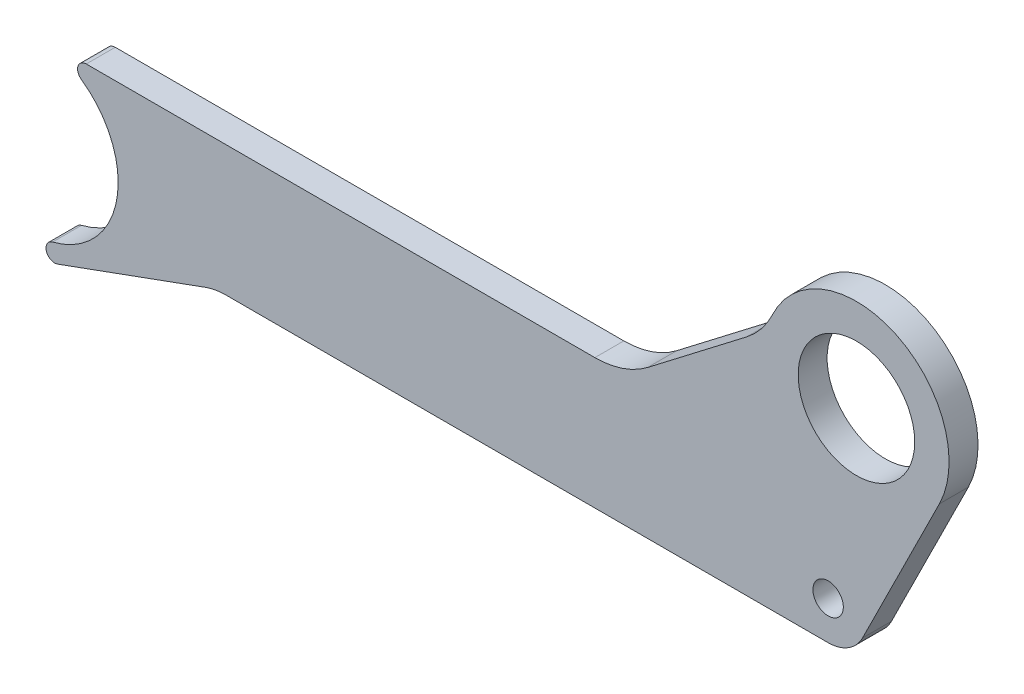
SolidWorks part; units mm, degrees
ref_plane "Plane1" through (0, 0, 0) normal (0, 0, 1) x (1, 0, 0)
ref_plane "Plane2" through (0, 0, 0) normal (0, 1, 0) x (1, 0, 0)
ref_plane "Plane3" through (0, 0, 0) normal (1, 0, 0) x (0, 0, -1)
sketch "Sketch1" plane through (0, 0, 0) normal (0, 0, 1) x (1, 0, 0)
  line L0 (-37.9234, 2.4122) -> (-72.0845, -23.8006)
  line L1 (-90.3474, -30) -> (-266.0263, -30)
  line L2 (2.1045, -67.6387) -> (28.6531, -14.2478)
  line L3 (-217.9327, -75) -> (-9.7772, -75)
  line L4 (-9.7772, -61.7305) -> (0, 0) construction
  line L5 (0, 0) -> (134, 0) construction
  line L8 (-275.9117, -94.8191) -> (-224.7731, -76.2061)
  line L9 (0, 0) -> (-76.4334, -58.6494) construction
  circle A0 centre (0, 0) radius 20.125
  arc A1 (28.6531, -14.2478) -> (-28.9993, 13.5292) centre (0, 0) ccw
  arc A2 (-267.7512, -35.4545) -> (-277.6707, -89.0909) centre (-285, -60) cw
  arc A3 (-266.0263, -30) -> (-267.7512, -35.4545) centre (-266.0263, -33) ccw
  arc A4 (-277.6707, -89.0909) -> (-275.9117, -94.8191) centre (-276.9377, -92) ccw
  circle A5 centre (-9.7772, -61.7305) radius 5.25
  arc A6 (-9.7772, -75) -> (2.1045, -67.6387) centre (-9.7772, -61.7305) ccw
  arc A9 (-217.9327, -75) -> (-224.7731, -76.2061) centre (-217.9327, -95) ccw
  arc A13 (-37.9234, 2.4122) -> (-28.9993, 13.5292) centre (-56.1862, 26.2128) ccw
  arc A15 (-72.0845, -23.8006) -> (-90.3474, -30) centre (-90.3474, 0) cw
  dimension "D1" = 40.25
  dimension "D2" = 32
  dimension "D6" = 30
  dimension "D9" = 3
  dimension "D10" = 20
  dimension "D13" = 291.2473
  dimension "D14" = 99
  dimension "D16" = 62.5
  dimension "D18" = 65
  dimension "D21" = 30
  dimension "D17" = 3
  dimension "D11" = 20
  dimension "D19" = 10.5
  dimension "D3" = 37.5
  dimension "D4" = 45
  dimension "D5" = 30
  dimension "D7" = 60
  dimension "D8" = 285
  dimension "D20" = 25
extrude "Extrude1" add sketch "Sketch1" along normal blind 10
ref_plane "Plane4" through (0, 0, 0) normal (0.206, -0.9785, 0) x (0.9785, 0.206, 0)
ref_plane "Plane5" through (0, 0, 0) normal (-0.9785, -0.206, 0) x (0, 0, 1)
